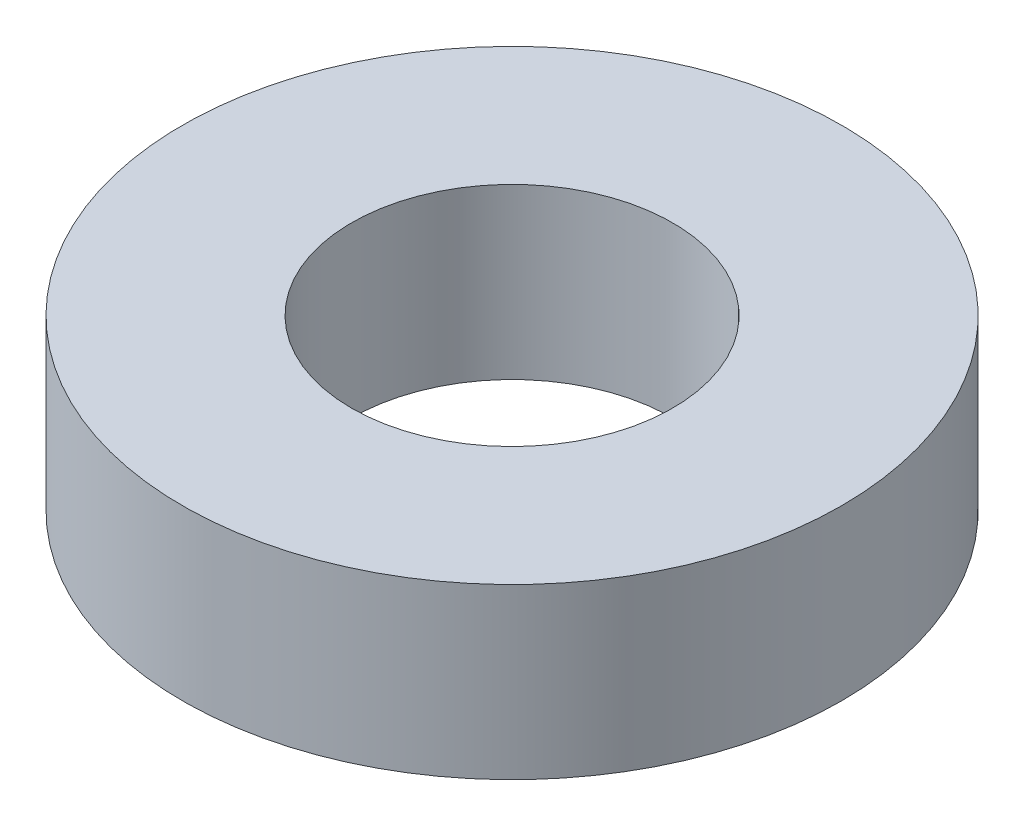
SolidWorks part; units mm, degrees
ref_plane "前视基准面" through (0, 0, 0) normal (0, 0, 1) x (1, 0, 0)
ref_plane "上视基准面" through (0, 0, 0) normal (0, 1, 0) x (1, 0, 0)
ref_plane "右视基准面" through (0, 0, 0) normal (1, 0, 0) x (0, 0, -1)
other "Configuration Table"
sketch "草图1" plane through (0, 0, 0) normal (0, 1, 0) x (1, 0, 0)
  circle A0 centre (0, 0) radius 1.9
  dimension "D1" = 3.8
extrude "拉伸-薄壁1" add sketch "草图1" along normal blind 2 thin
